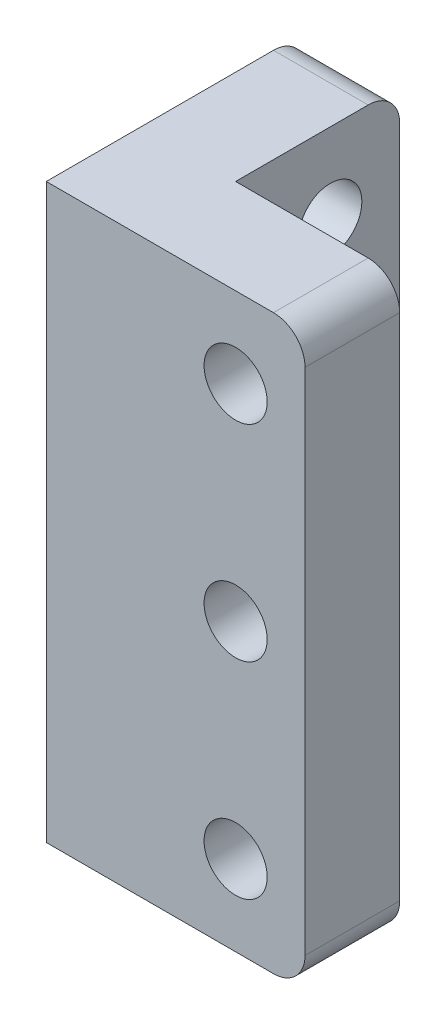
SolidWorks part; units mm, degrees
ref_plane "Front Plane" through (0, 0, 0) normal (0, 0, 1) x (1, 0, 0)
ref_plane "Top Plane" through (0, 0, 0) normal (0, 1, 0) x (1, 0, 0)
ref_plane "Right Plane" through (0, 0, 0) normal (1, 0, 0) x (0, 0, -1)
sketch "Sketch1" plane through (0, 0, 0) normal (0, 1, 0) x (1, 0, 0)
  line L0 (0, 0) -> (0, 5.2)
  line L1 (0, 5.2) -> (-3, 5.2)
  line L2 (-3, 5.2) -> (-3, -3)
  line L3 (-3, -3) -> (5.2, -3)
  line L4 (5.2, -3) -> (5.2, 0)
  line L5 (0, 0) -> (5.2, 0)
  dimension "D1" = 5.2
  dimension "D2" = 3
  dimension "D3" = 8.2
  dimension "D4" = 8.2
  dimension "D5" = 3
extrude "Boss-Extrude1" add sketch "Sketch1" along normal blind 18.14
fillet "Fillet1" radius 1 4 edges at (5.2, 0, 1.5) (5.2, 18.14, 1.5) (-1.5, 0, -5.2) (-1.5, 18.14, -5.2)
sketch "Sketch3" plane through (0, 0, 0) normal (1, 0, 0) x (0, 0, -1)
  line L1 (0, 18.14) -> (4.2, 18.14) construction
  line L2 (0, 18.14) -> (0, 0) construction
  circle A0 centre (3, 15.59) radius 1
  point P0 (3, 15.59)
  dimension "D3" = 2
  dimension "D1" = 3
  dimension "D2" = 2.55
extrude "Cut-Extrude1" cut sketch "Sketch3" against normal blind 5.1
sketch "Sketch4" plane through (0, 0, 0) normal (0, 0, -1) x (-1, 0, 0)
  line L0 (-4.2, 0) -> (0, 0) construction
  line L1 (0, 18.14) -> (0, 0) construction
  circle A0 centre (-3, 2.55) radius 1
  point P0 (-3, 2.55)
  dimension "D3" = 2
  dimension "D1" = 2.55
  dimension "D2" = 3
extrude "Cut-Extrude2" cut sketch "Sketch4" against normal blind 5.1
sketch "Sketch5" plane through (0, 0, 0) normal (0, 0, -1) x (-1, 0, 0)
  circle A0 centre (-3, 2.55) radius 1.7
  dimension "D1" = 3.4
extrude "Cut-Extrude3" cut sketch "Sketch5" against normal blind 1.4
sketch "Sketch6" plane through (-3, 0, 0) normal (-1, 0, 0) x (0, 0, 1)
  circle A0 centre (-3, 15.59) radius 1.7
  dimension "D1" = 3.4
extrude "Cut-Extrude4" cut sketch "Sketch6" against normal blind 1.4
ref_plane "Plane1" through (0, 9.07, 0) normal (0, 1, 0) x (1, 0, 0)
mirror "Mirror2" about plane through (0, 9.07, 0) normal (0, 1, 0) of "Cut-Extrude4", "Cut-Extrude3", "Cut-Extrude2", "Cut-Extrude1"
pattern_linear "LPattern1" count 2 spacing 6.52 along (0, -1, 0) of "Cut-Extrude1", "Cut-Extrude4"
pattern_linear "LPattern2" count 2 spacing 6.52 along (0, 1, 0) of "Cut-Extrude3", "Cut-Extrude2"
